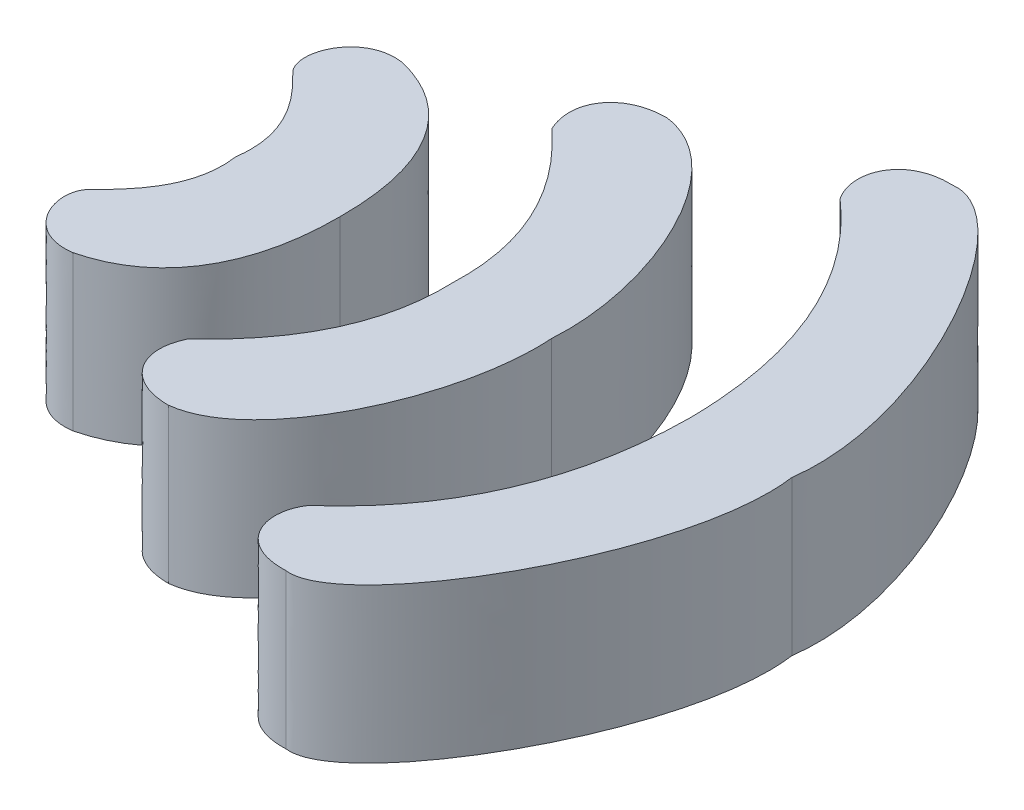
SolidWorks part; units mm, degrees
ref_plane "Front Plane" through (0, 0, 0) normal (0, 0, 1) x (1, 0, 0)
ref_plane "Top Plane" through (0, 0, 0) normal (0, 1, 0) x (1, 0, 0)
ref_plane "Right Plane" through (0, 0, 0) normal (1, 0, 0) x (0, 0, -1)
sketch "Sketch1" plane through (0, 0, 0) normal (0, 1, 0) x (1, 0, 0)
  line L0 (1.5499, 5.0558) -> (10.0589, 5.0558) construction
  line L1 (1.5499, 5.0558) -> (0, 5.0558) construction
  spline S0 degree 3 poles (0.9641, 6.3763) (1.3382, 6.0228) (1.6296, 5.6137) (1.5499, 5.0558) knots 0 0 0 0 1 1 1 1
  spline S1 degree 3 poles (0.9641, 6.3763) (0.7398, 6.6296) (0.9972, 7.2731) (1.5711, 7.1895) knots 0 0 0 0 1 1 1 1
  spline S2 degree 3 poles (1.5711, 7.1895) (2.506, 6.9577) (2.9043, 6.1194) (2.8967, 5.0558) knots 0 0 0 0 1 1 1 1
  spline S3 degree 2 poles (4.3673, 5.0558) (4.4198, 6.3703) (3.285, 7.4103) knots 0 0 0 1 1 1
  spline S4 degree 3 poles (3.285, 7.4103) (3.0683, 7.8569) (3.3481, 8.2825) (3.8997, 8.2825) knots 0 0 0 0 1 1 1 1
  spline S5 degree 3 poles (3.8997, 8.2825) (4.8914, 8.1708) (5.7254, 6.3178) (5.6335, 5.0558) knots 0 0 0 0 1 1 1 1
  spline S6 degree 3 poles (7.4213, 5.0558) (7.4106, 6.3991) (6.9676, 7.5916) (5.9369, 8.4934) knots 0 0 0 0 1 1 1 1
  spline S7 degree 3 poles (5.9369, 8.4934) (5.6884, 8.8535) (5.8714, 9.4041) (6.52, 9.3773) knots 0 0 0 0 1 1 1 1
  spline S8 degree 3 poles (6.52, 9.3773) (7.338, 9.4823) (8.9747, 6.6557) (8.7493, 5.0558) knots 0 0 0 0 1 1 1 1
  spline S9 degree 3 poles (6.52, 0.7343) (7.338, 0.6293) (8.9747, 3.4559) (8.7493, 5.0558) knots 0 0 0 0 1 1 1 1
  spline S10 degree 3 poles (5.9369, 1.6182) (5.6884, 1.258) (5.8714, 0.7075) (6.52, 0.7343) knots 0 0 0 0 1 1 1 1
  spline S11 degree 3 poles (7.4213, 5.0558) (7.4106, 3.7125) (6.9676, 2.52) (5.9369, 1.6182) knots 0 0 0 0 1 1 1 1
  spline S12 degree 3 poles (3.8997, 1.8291) (4.8914, 1.9408) (5.7254, 3.7938) (5.6335, 5.0558) knots 0 0 0 0 1 1 1 1
  spline S13 degree 3 poles (3.285, 2.7013) (3.0683, 2.2547) (3.3481, 1.8291) (3.8997, 1.8291) knots 0 0 0 0 1 1 1 1
  spline S14 degree 2 poles (4.3673, 5.0558) (4.4198, 3.7413) (3.285, 2.7013) knots 0 0 0 1 1 1
  spline S15 degree 3 poles (1.5711, 2.9221) (2.506, 3.1539) (2.9043, 3.9922) (2.8967, 5.0558) knots 0 0 0 0 1 1 1 1
  spline S16 degree 3 poles (0.9641, 3.7353) (0.7398, 3.482) (0.9972, 2.8384) (1.5711, 2.9221) knots 0 0 0 0 1 1 1 1
  spline S17 degree 3 poles (0.9641, 3.7353) (1.3382, 4.0888) (1.6296, 4.4979) (1.5499, 5.0558) knots 0 0 0 0 1 1 1 1
extrude "Boss-Extrude1" add sketch "Sketch1" along normal blind 2
